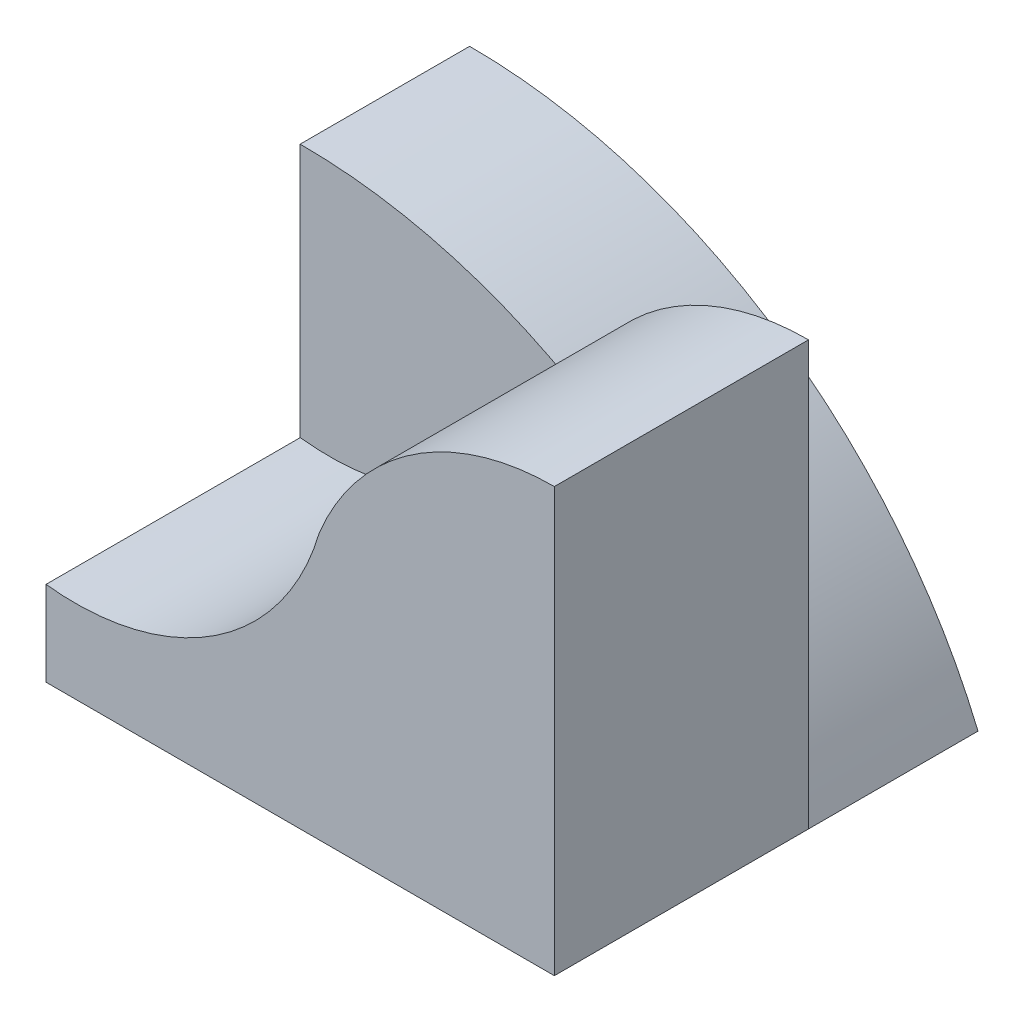
SolidWorks part; units mm, degrees
ref_plane "Front Plane" through (0, 0, 0) normal (0, 0, 1) x (1, 0, 0)
ref_plane "Top Plane" through (0, 0, 0) normal (0, 1, 0) x (1, 0, 0)
ref_plane "Right Plane" through (0, 0, 0) normal (1, 0, 0) x (0, 0, -1)
sketch "Sketch1" plane through (0, 0, 0) normal (0, 0, 1) x (1, 0, 0)
  line L0 (0, 20) -> (0, 0)
  line L1 (0, 0) -> (30, 0)
  arc A0 (0, 20) -> (30, 0) centre (0, -12.5) cw
  dimension "D1" = 20
  dimension "D2" = 30
extrude "Boss-Extrude1" add sketch "Sketch1" along normal blind 10
sketch "Sketch2" plane through (0, 0, 10) normal (0, 0, 1) x (1, 0, 0)
  line L0 (0, 5) -> (0, 0)
  line L1 (0, 20) -> (0, 0) construction
  line L2 (0, 0) -> (30, 0)
  line L3 (30, 0) -> (30, 25)
  arc A0 (30, 25) -> (16.131, 15.7142) centre (30, 10) ccw
  arc A1 (30, 0) -> (0, 20) centre (0, -12.5) ccw construction
  arc A2 (16.131, 15.7142) -> (0, 5) centre (1.727, 19.9003) cw
  dimension "D1" = 15
  dimension "D3" = 5
  dimension "D4" = 15
  dimension "D2" = 25
extrude "Boss-Extrude5" add sketch "Sketch2" along normal blind 15
